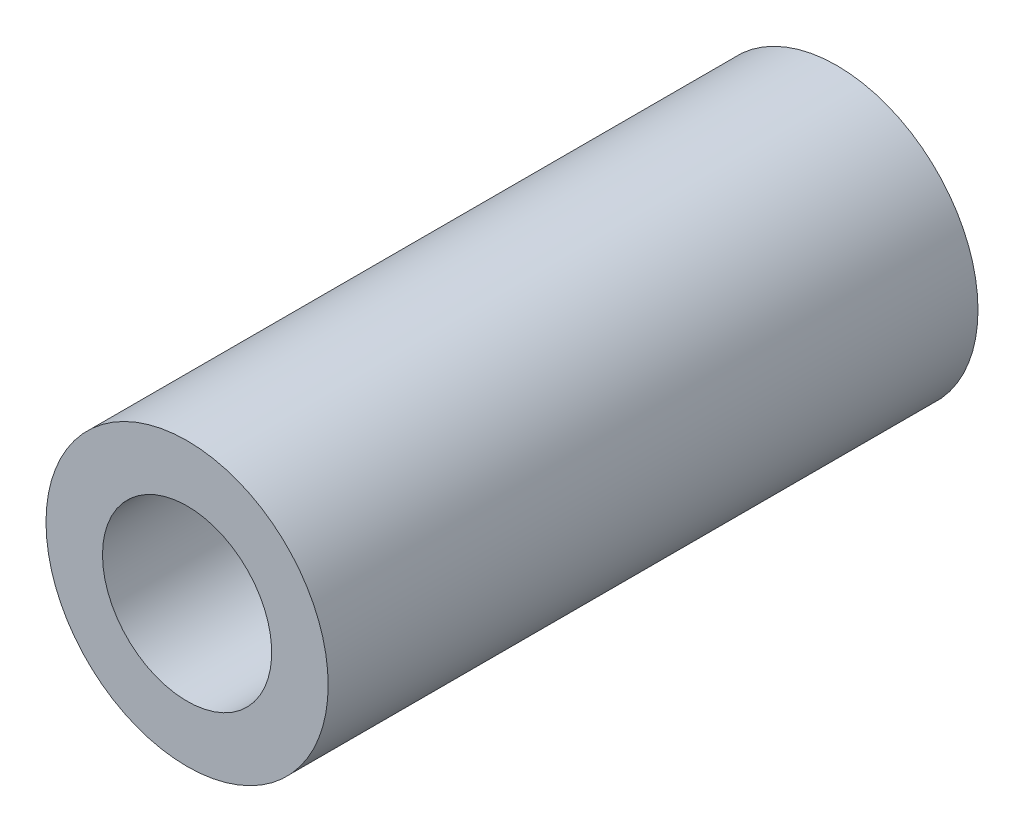
SolidWorks part; units mm, degrees
ref_plane "Front Plane" through (0, 0, 0) normal (0, 0, 1) x (1, 0, 0)
ref_plane "Top Plane" through (0, 0, 0) normal (0, 1, 0) x (1, 0, 0)
ref_plane "Right Plane" through (0, 0, 0) normal (1, 0, 0) x (0, 0, -1)
sketch "Sketch1" plane through (0, 0, 0) normal (0, 0, 1) x (1, 0, 0)
  circle A0 centre (0, 0) radius 31.7101
extrude "Boss-Extrude1" add sketch "Sketch1" along normal blind 146.05
sketch "Sketch2" plane through (0, 0, 0) normal (0, 0, -1) x (-1, 0, 0)
  circle A0 centre (0, 0) radius 19.014
extrude "Cut-Extrude1" cut sketch "Sketch2" against normal blind 146.05
